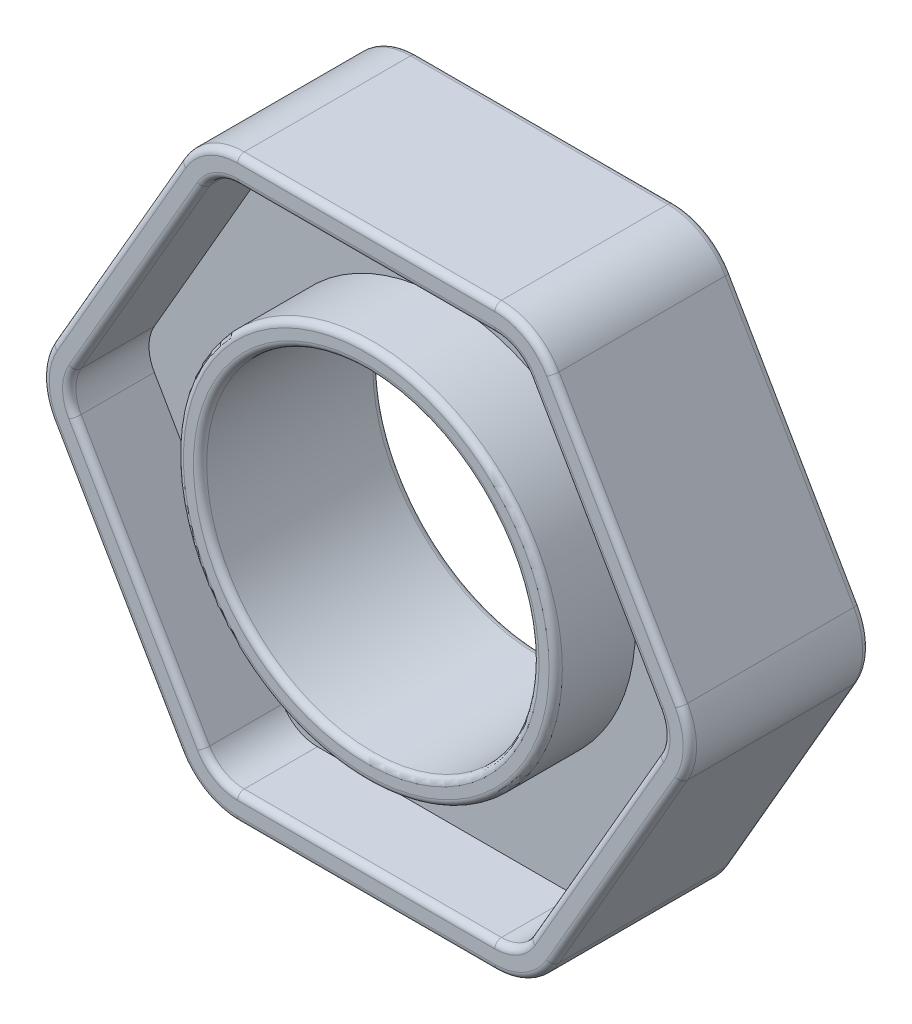
SolidWorks part; units mm, degrees
ref_plane "前基準面" through (0, 0, 0) normal (0, 0, 1) x (1, 0, 0)
ref_plane "上基準面" through (0, 0, 0) normal (0, 1, 0) x (1, 0, 0)
ref_plane "右基準面" through (0, 0, 0) normal (1, 0, 0) x (0, 0, -1)
sketch "草圖1" plane through (0, 0, 0) normal (0, 0, 1) x (1, 0, 0)
  line L1 (23.6714, 2.5) -> (14.0007, 19.25)
  line L2 (9.6706, 21.75) -> (-9.6706, 21.75)
  line L3 (-14.0007, 19.25) -> (-23.6714, 2.5)
  line L4 (-23.6714, -2.5) -> (-14.0007, -19.25)
  line L5 (-9.6706, -21.75) -> (9.6706, -21.75)
  line L6 (14.0007, -19.25) -> (23.6714, -2.5)
  circle A0 centre (0, 0) radius 21.75 construction
  arc A1 (14.0007, 19.25) -> (9.6706, 21.75) centre (9.6706, 16.75) ccw
  arc A2 (23.6714, 2.5) -> (23.6714, -2.5) centre (19.3412, 0) cw
  arc A3 (9.6706, -21.75) -> (14.0007, -19.25) centre (9.6706, -16.75) ccw
  arc A4 (-14.0007, -19.25) -> (-9.6706, -21.75) centre (-9.6706, -16.75) ccw
  arc A5 (-23.6714, 2.5) -> (-23.6714, -2.5) centre (-19.3412, 0) ccw
  arc A6 (-9.6706, 21.75) -> (-14.0007, 19.25) centre (-9.6706, 16.75) ccw
  point P21 (0, 0)
  dimension "D2" = 5
  dimension "D1" = 43.5
extrude "填料-伸長1" add sketch "草圖1" along normal blind 13.5
sketch "草圖2" plane through (0, 0, 13.5) normal (0, 0, 1) x (1, 0, 0)
  line L12 (9.6706, 19.75) -> (-9.6706, 19.75)
  line L13 (-12.2687, 18.25) -> (-21.9393, 1.5)
  line L14 (-21.9393, -1.5) -> (-12.2687, -18.25)
  line L15 (-9.6706, -19.75) -> (9.6706, -19.75)
  line L16 (12.2687, -18.25) -> (21.9393, -1.5)
  line L17 (21.9393, 1.5) -> (12.2687, 18.25)
  line L18 (9.6706, 19.75) -> (-9.6706, 19.75)
  line L19 (-12.2687, 18.25) -> (-21.9393, 1.5)
  line L20 (-21.9393, -1.5) -> (-12.2687, -18.25)
  line L21 (-9.6706, -19.75) -> (9.6706, -19.75)
  line L22 (12.2687, -18.25) -> (21.9393, -1.5)
  line L23 (21.9393, 1.5) -> (12.2687, 18.25)
  arc A12 (12.2687, 18.25) -> (9.6706, 19.75) centre (9.6706, 16.75) ccw
  arc A13 (-9.6706, 19.75) -> (-12.2687, 18.25) centre (-9.6706, 16.75) ccw
  arc A14 (-21.9393, 1.5) -> (-21.9393, -1.5) centre (-19.3412, 0) ccw
  arc A15 (-12.2687, -18.25) -> (-9.6706, -19.75) centre (-9.6706, -16.75) ccw
  arc A16 (9.6706, -19.75) -> (12.2687, -18.25) centre (9.6706, -16.75) ccw
  arc A17 (21.9393, -1.5) -> (21.9393, 1.5) centre (19.3412, 0) ccw
  arc A18 (12.2687, 18.25) -> (9.6706, 19.75) centre (9.6706, 16.75) ccw
  arc A19 (-9.6706, 19.75) -> (-12.2687, 18.25) centre (-9.6706, 16.75) ccw
  arc A20 (-21.9393, 1.5) -> (-21.9393, -1.5) centre (-19.3412, 0) ccw
  arc A21 (-12.2687, -18.25) -> (-9.6706, -19.75) centre (-9.6706, -16.75) ccw
  arc A22 (9.6706, -19.75) -> (12.2687, -18.25) centre (9.6706, -16.75) ccw
  arc A23 (21.9393, -1.5) -> (21.9393, 1.5) centre (19.3412, 0) ccw
  dimension "D1" = 2
extrude "除料-伸長1" cut sketch "草圖2" against normal blind 6
sketch "草圖3" plane through (0, 0, 0) normal (0, 0, -1) x (-1, 0, 0)
  line L12 (-12.2687, 18.25) -> (-21.9393, 1.5)
  line L13 (-21.9393, -1.5) -> (-12.2687, -18.25)
  line L14 (-9.6706, -19.75) -> (9.6706, -19.75)
  line L15 (12.2687, -18.25) -> (21.9393, -1.5)
  line L16 (21.9393, 1.5) -> (12.2687, 18.25)
  line L17 (9.6706, 19.75) -> (-9.6706, 19.75)
  line L18 (-12.2687, 18.25) -> (-21.9393, 1.5)
  line L19 (-21.9393, -1.5) -> (-12.2687, -18.25)
  line L20 (-9.6706, -19.75) -> (9.6706, -19.75)
  line L21 (12.2687, -18.25) -> (21.9393, -1.5)
  line L22 (21.9393, 1.5) -> (12.2687, 18.25)
  line L23 (9.6706, 19.75) -> (-9.6706, 19.75)
  arc A12 (-9.6706, 19.75) -> (-12.2687, 18.25) centre (-9.6706, 16.75) ccw
  arc A13 (-21.9393, 1.5) -> (-21.9393, -1.5) centre (-19.3412, 0) ccw
  arc A14 (-12.2687, -18.25) -> (-9.6706, -19.75) centre (-9.6706, -16.75) ccw
  arc A15 (9.6706, -19.75) -> (12.2687, -18.25) centre (9.6706, -16.75) ccw
  arc A16 (21.9393, -1.5) -> (21.9393, 1.5) centre (19.3412, 0) ccw
  arc A17 (12.2687, 18.25) -> (9.6706, 19.75) centre (9.6706, 16.75) ccw
  arc A18 (-9.6706, 19.75) -> (-12.2687, 18.25) centre (-9.6706, 16.75) ccw
  arc A19 (-21.9393, 1.5) -> (-21.9393, -1.5) centre (-19.3412, 0) ccw
  arc A20 (-12.2687, -18.25) -> (-9.6706, -19.75) centre (-9.6706, -16.75) ccw
  arc A21 (9.6706, -19.75) -> (12.2687, -18.25) centre (9.6706, -16.75) ccw
  arc A22 (21.9393, -1.5) -> (21.9393, 1.5) centre (19.3412, 0) ccw
  arc A23 (12.2687, 18.25) -> (9.6706, 19.75) centre (9.6706, 16.75) ccw
  dimension "D1" = 2
extrude "除料-伸長2" cut sketch "草圖3" against normal blind 6
sketch "草圖4" plane through (0, 0, 6) normal (0, 0, -1) x (-1, 0, 0)
  circle A0 centre (0, 0) radius 14.25
  dimension "D1" = 28.5
extrude "填料-伸長2" add sketch "草圖4" along normal up to surface and the other way up to surface
sketch "草圖5" plane through (0, 0, 13.5) normal (0, 0, 1) x (1, 0, 0)
  circle A0 centre (0, 0) radius 12.5
  dimension "D1" = 25
extrude "除料-伸長3" cut sketch "草圖5" against normal up to next
fillet "圓角1" radius 0.5 52 edges at (-22.3412, 0, 0) (-17.104, -9.875, 0) (-11.1706, -19.3481, 0) (0, -19.75, 0) (11.1706, -19.3481, 0) (17.104, -9.875, 0) (22.3412, 0, 0) (17.104, 9.875, 0) (11.1706, 19.3481, 0) (0, 19.75, 0) (-11.1706, 19.3481, 0) (-12.1706, 21.0801, 0) (0, 21.75, 0) (12.1706, 21.0801, 0) (18.8361, 10.875, 0) (24.3412, 0, 0) (18.8361, -10.875, 0) (12.1706, -21.0801, 0) (0, -21.75, 0) (-12.1706, -21.0801, 0) (-18.8361, -10.875, 0) (-24.3412, 0, 0) (-11.1706, 19.3481, 13.5) (0, 19.75, 13.5) (11.1706, 19.3481, 13.5) (17.104, 9.875, 13.5) (22.3412, 0, 13.5) (17.104, -9.875, 13.5) (11.1706, -19.3481, 13.5) (0, -19.75, 13.5) (-11.1706, -19.3481, 13.5) (-17.104, -9.875, 13.5) (-22.3412, 0, 13.5) (-12.1706, 21.0801, 13.5) (0, 21.75, 13.5) (12.1706, 21.0801, 13.5) (18.8361, 10.875, 13.5) (24.3412, 0, 13.5) (18.8361, -10.875, 13.5) (12.1706, -21.0801, 13.5) (0, -21.75, 13.5) (-12.1706, -21.0801, 13.5) (-18.8361, -10.875, 13.5) (-24.3412, 0, 13.5) (14.25, 0, 0) (-17.104, 9.875, 0) (-18.8361, 10.875, 0) (12.5, 0, 0) (12.5, 0, 13.5) (14.25, 0, 13.5) (-17.104, 9.875, 13.5) (-18.8361, 10.875, 13.5)
